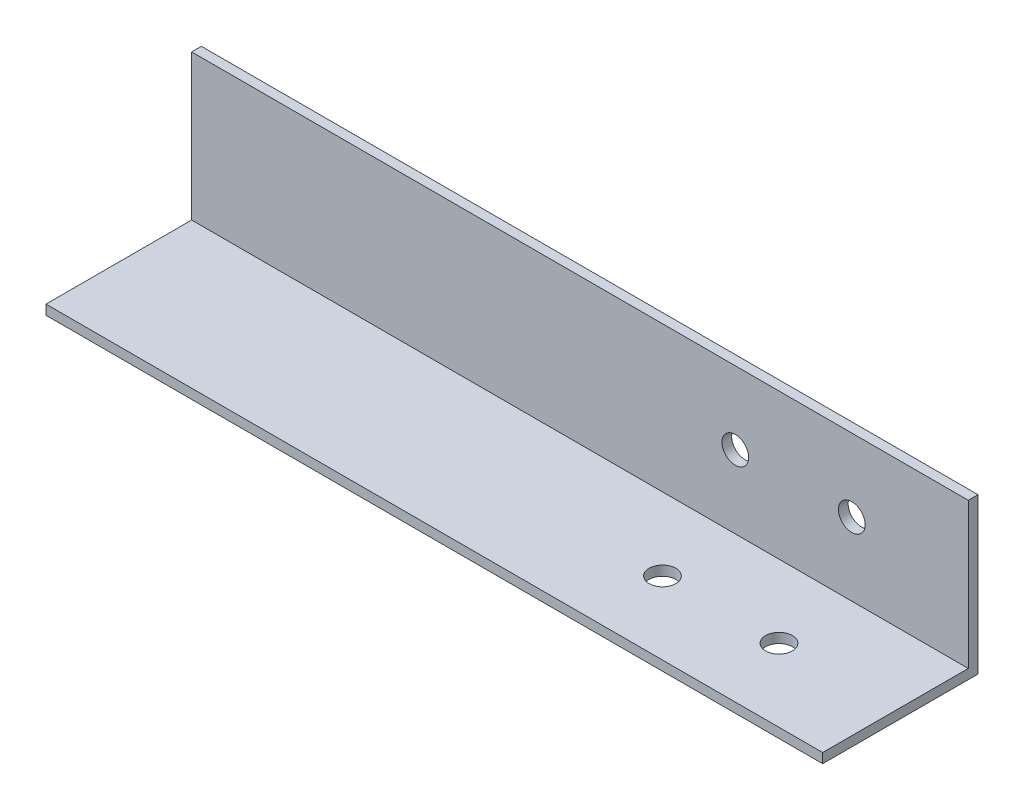
SolidWorks part; units mm, degrees
ref_plane "Front Plane" through (0, 0, 0) normal (0, 0, 1) x (1, 0, 0)
ref_plane "Top Plane" through (0, 0, 0) normal (0, 1, 0) x (1, 0, 0)
ref_plane "Right Plane" through (0, 0, 0) normal (1, 0, 0) x (0, 0, -1)
sketch "Sketch1" plane through (0, 0, 0) normal (1, 0, 0) x (0, 0, -1)
  line L1 (-3.175, 0) -> (-50.8, 0)
  line L2 (0, 0) -> (0, -3.175)
  line L3 (0, -3.175) -> (-50.8, -3.175)
  line L4 (-50.8, 0) -> (-50.8, -3.175)
  line L6 (0, 0) -> (0, 47.625)
  line L7 (0, 47.625) -> (-3.175, 47.625)
  line L8 (-3.175, 0) -> (-3.175, 47.625)
  dimension "D1" = 3.175
  dimension "D2" = 50.8
  dimension "D3" = 50.8
  dimension "D4" = 3.175
extrude "Boss-Extrude1" add sketch "Sketch1" along normal blind 254
sketch "Sketch2" plane through (0, 0, 3.175) normal (0, 0, 1) x (1, 0, 0)
  line L0 (254, 23.8125) -> (0, 23.8125) construction
  line L1 (254, 47.625) -> (254, 0) construction
  line L2 (0, 47.625) -> (0, 0) construction
  circle A0 centre (177.8, 23.8125) radius 4.3656
  circle A1 centre (215.9, 23.8125) radius 4.3656
  dimension "D1" = 8.7312
  dimension "D2" = 38.1
  dimension "D3" = 38.1
extrude "Cut-Extrude1" cut sketch "Sketch2" against normal up to surface (3.175 mm away) up to face at (127, 22.225, 0)
sketch "Sketch3" plane through (0, 0, 0) normal (0, 1, 0) x (1, 0, 0)
  line L0 (0, -26.9875) -> (254, -26.9875) construction
  line L1 (0, -3.175) -> (0, -50.8) construction
  line L2 (254, -3.175) -> (254, -50.8) construction
  circle A0 centre (177.8, -26.9875) radius 4.3656
  circle A1 centre (215.9, -26.9875) radius 4.3656
  dimension "D1" = 8.7312
  dimension "D2" = 38.1
  dimension "D3" = 38.1
extrude "Cut-Extrude2" cut sketch "Sketch3" against normal up to surface (3.175 mm away) up to face at (127, -3.175, 25.4)
